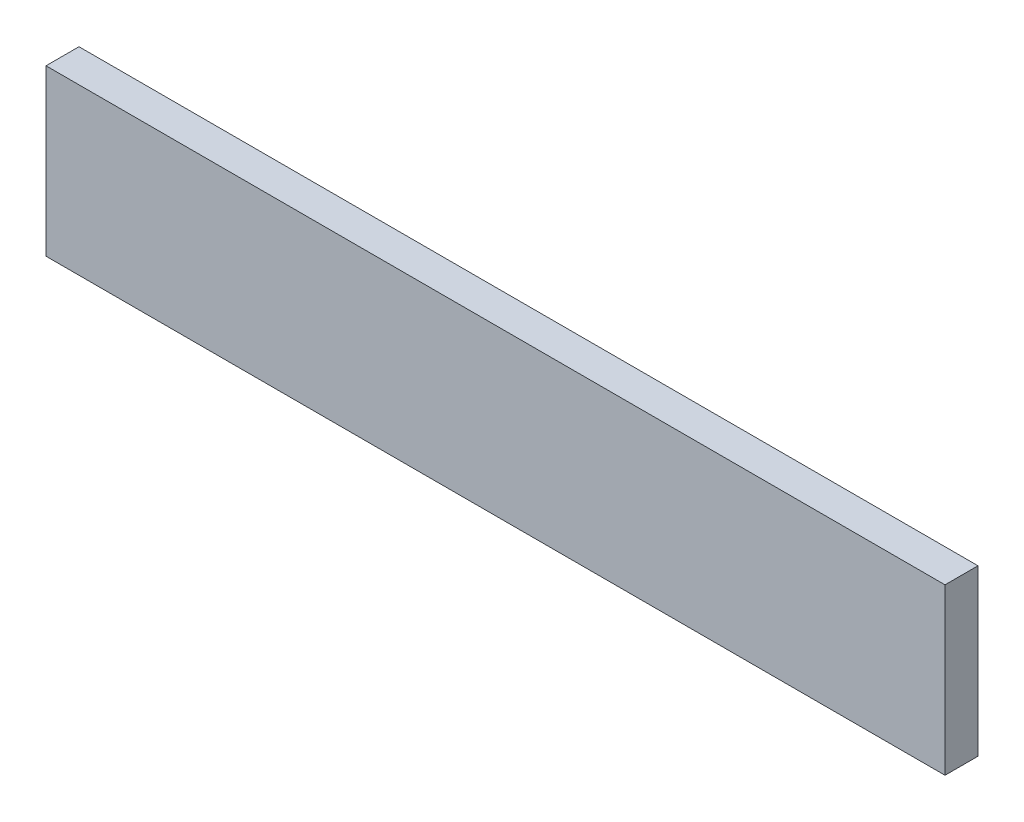
SolidWorks part; units mm, degrees
ref_plane "Front Plane" through (0, 0, 0) normal (0, 0, 1) x (1, 0, 0)
ref_plane "Top Plane" through (0, 0, 0) normal (0, 1, 0) x (1, 0, 0)
ref_plane "Right Plane" through (0, 0, 0) normal (1, 0, 0) x (0, 0, -1)
sketch "Sketch1" plane through (0, 0, 0) normal (0, 0, 1) x (1, 0, 0)
  line L1 (0, 0) -> (138.43, 0)
  line L2 (0, 0) -> (0, 25.4)
  line L3 (0, 25.4) -> (138.43, 25.4)
  line L4 (138.43, 0) -> (138.43, 25.4)
  dimension "D1" = 25.4
  dimension "D2" = 138.43
extrude "Boss-Extrude1" add sketch "Sketch1" along normal blind 5.08
equation "\"GMaterial\" = 0.21in"
equation "\"MDF\"= 0.21in"
equation "\"Foamcore\"= 0.2in"
equation "\"D1@Boss-Extrude1\"=\"Foamcore\""
